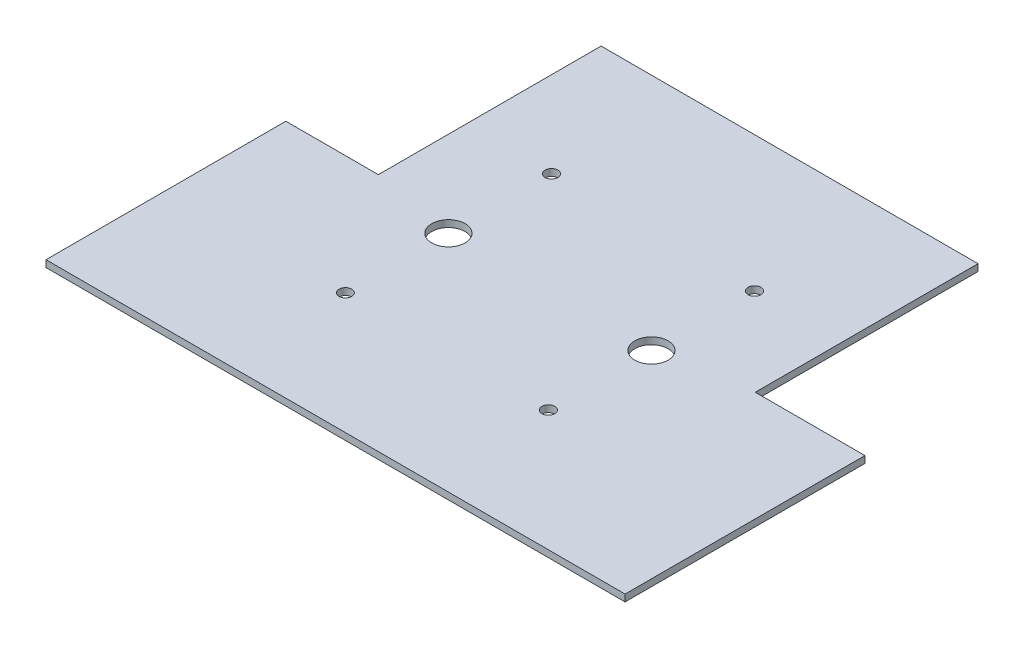
SolidWorks part; units mm, degrees
ref_plane "Front" through (0, 0, 0) normal (0, 0, 1) x (1, 0, 0)
ref_plane "Top" through (0, 0, 0) normal (0, 1, 0) x (1, 0, 0)
ref_plane "Right" through (0, 0, 0) normal (1, 0, 0) x (0, 0, -1)
sketch "Skizze1" plane through (0, 0, 0) normal (0, 1, 0) x (1, 0, 0)
  line L0 (142, -65) -> (110, -65)
  line L4 (110, 0) -> (110, -65)
  line L6 (142, -65) -> (142, -135)
  line L7 (142, -135) -> (-27, -135)
  line L8 (-27, -65) -> (-27, -135)
  line L9 (0, -65) -> (0, 0)
  line L10 (0, 0) -> (110, 0)
  line L11 (0, -65) -> (-27, -65)
  point P5 (67.5, -95)
  point P10 (0, 0)
  point P12 (0, 0)
  dimension "D1" = 110
  dimension "D2" = 169
  dimension "D3" = 70
  dimension "D4" = 32
  dimension "D5" = 27
  dimension "D6" = 65
  dimension "D7" = 65
extrude "Aufsatz-Linear austragen1" add sketch "Skizze1" along normal blind 2
sketch "Skizze2" plane through (0, 2, 0) normal (0, 1, 0) x (1, 0, 0)
  circle A0 centre (25.0441, -69.5979) radius 4.875
extrude "Schnitt-Linear austragen1" cut sketch "Skizze2" against normal blind 2
sketch "Skizze3" plane through (0, 2, 0) normal (0, 1, 0) x (1, 0, 0)
  circle A0 centre (84.2941, -69.5979) radius 4.875
extrude "Schnitt-Linear austragen2" cut sketch "Skizze3" against normal blind 2
sketch "Skizze4" plane through (0, 2, 0) normal (0, 1, 0) x (1, 0, 0)
  circle A0 centre (84.2941, -99.6729) radius 1.875
extrude "Schnitt-Linear austragen3" cut sketch "Skizze4" against normal blind 2
sketch "Skizze5" plane through (0, 2, 0) normal (0, 1, 0) x (1, 0, 0)
  circle A0 centre (25.0441, -99.6729) radius 1.8453
extrude "Schnitt-Linear austragen4" cut sketch "Skizze5" against normal blind 2
sketch "Skizze6" plane through (0, 2, 0) normal (0, 1, 0) x (1, 0, 0)
  circle A0 centre (84.2941, -39.5229) radius 1.875
extrude "Schnitt-Linear austragen5" cut sketch "Skizze6" against normal blind 2
sketch "Skizze7" plane through (0, 2, 0) normal (0, 1, 0) x (1, 0, 0)
  circle A0 centre (25.0441, -39.5229) radius 1.875
extrude "Schnitt-Linear austragen6" cut sketch "Skizze7" against normal blind 2
